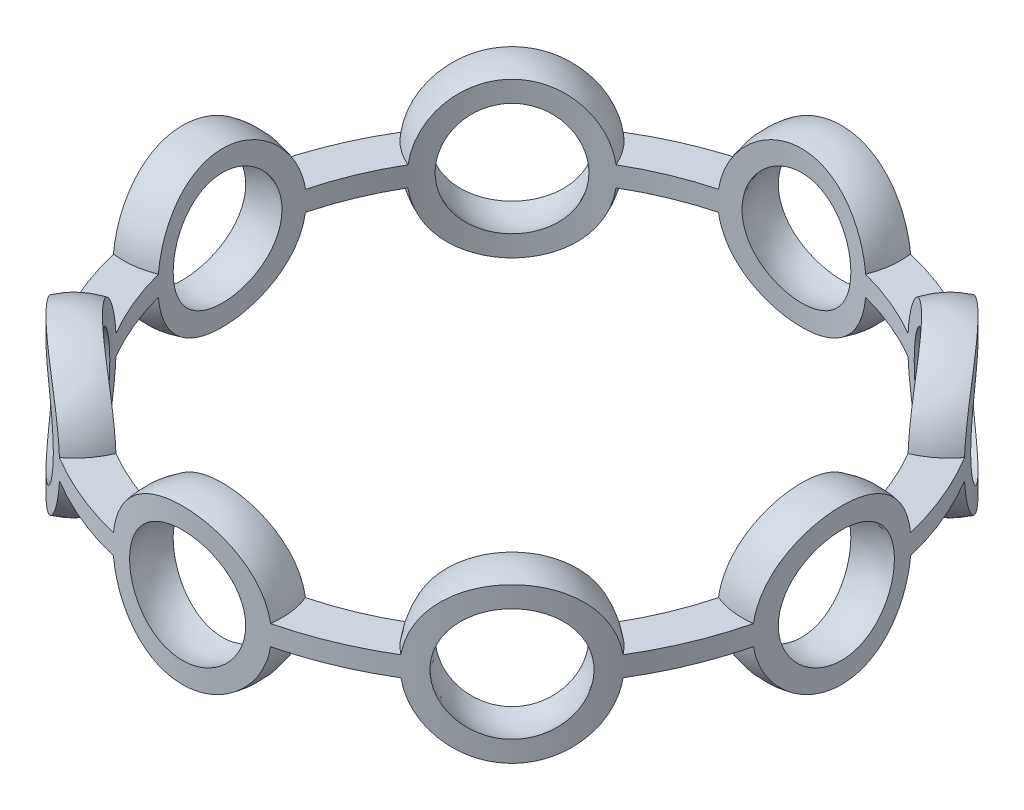
SolidWorks part; units mm, degrees
ref_plane "Front Plane" through (0, 0, 0) normal (0, 0, 1) x (1, 0, 0)
ref_plane "Top Plane" through (0, 0, 0) normal (0, 1, 0) x (1, 0, 0)
ref_plane "Right Plane" through (0, 0, 0) normal (1, 0, 0) x (0, 0, -1)
sketch "Sketch1" plane through (0, 0, 0) normal (0, 1, 0) x (1, 0, 0)
  circle A0 centre (0, 0) radius 14.5
  circle A1 centre (0, 0) radius 16.5
  dimension "D1" = 29
  dimension "D2" = 2
extrude "Boss-Extrude2" add sketch "Sketch1" along normal mid plane 8
sketch "Sketch7" plane through (0, 0, 0) normal (0, 0, 1) x (1, 0, 0)
  line L0 (-16.5, 4) -> (-16.5, -4) construction
  line L1 (-15.5, 4.6451) -> (-15.5, -4.6451)
  line L2 (-15.5, -4.6451) -> (-8.5314, -4.6451)
  line L4 (-15.5, 4.6451) -> (-8.5314, 4.6451)
  line L5 (-8.5314, -4.6451) -> (-8.5314, 4.6451)
  line L6 (-11.5, 0) -> (-8.5314, 0) construction
  line L7 (-11.5314, -0.5) -> (-8.5314, -0.5)
  line L8 (-15.5, 0) -> (-8.5314, -4.6451) construction
  line L9 (-15.5, 0) -> (-8.5314, 4.6451) construction
  line L10 (-11.5314, 0.5) -> (-8.5314, 0.5)
  line L11 (-12.068, 0.5) -> (-8.5314, 0.5) construction
  line L12 (-12.068, 0) -> (-8.5314, 0) construction
  line L13 (-12.068, -0.5) -> (-8.5314, -0.5) construction
  arc A2 (-15.5, -3) -> (-15.5, 3) centre (-15.5, 0) ccw
  arc A3 (-15.5, -4) -> (-15.5, 4) centre (-15.5, 0) ccw
  dimension "D1" = 1
  dimension "D2" = 0.5
  dimension "D3" = 0.5
  dimension "D4" = 3
revolve "Cut-Revolve7" cut sketch "Sketch7" angle 360 about L1
pattern_circular "CirPattern10" count 8 over 360 about axis through (0, 0, 0) along (0, 1, 0) of "Cut-Revolve7"
